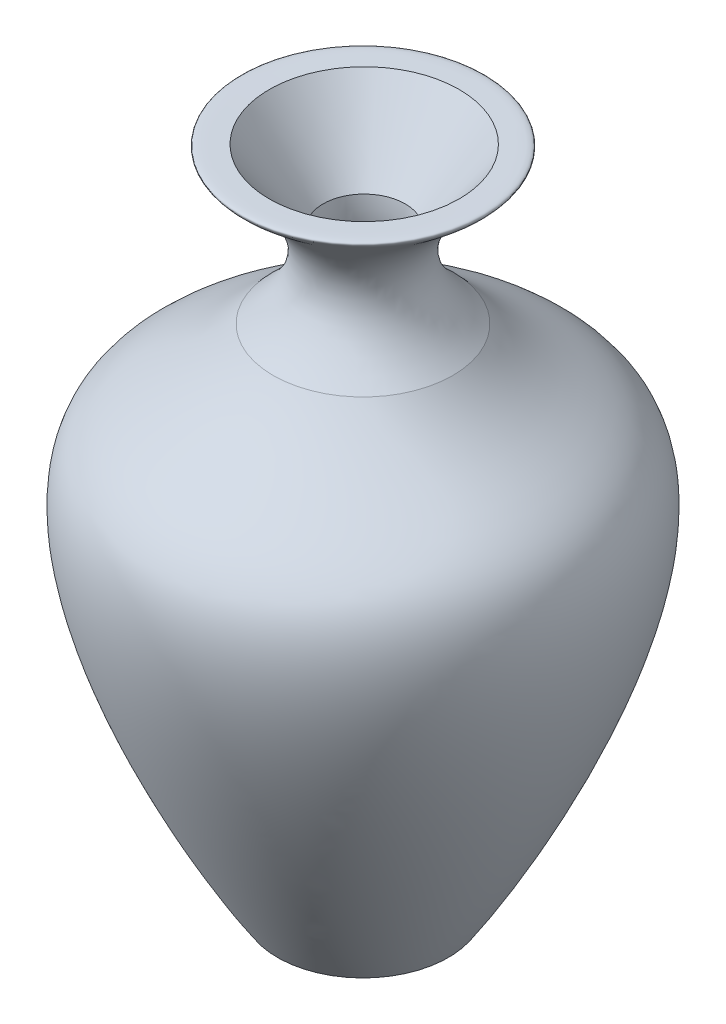
SolidWorks part; units mm, degrees
material "Ti-8Al-1Mo-1V annealed sheet (SS)"
ref_plane "Front Plane" through (0, 0, 0) normal (0, 0, 1) x (1, 0, 0)
ref_plane "Top Plane" through (0, 0, 0) normal (0, 1, 0) x (1, 0, 0)
ref_plane "Right Plane" through (0, 0, 0) normal (1, 0, 0) x (0, 0, -1)
sketch "Sketch1" plane through (0, 0, 0) normal (0, 0, 1) x (1, 0, 0)
  line L2 (-1.7649, 3.7152) -> (-5.8192, 3.7152)
  line L3 (-5.8192, 3.7152) -> (-5.8192, 35.1345)
  line L4 (-5.8192, 35.1345) -> (-2.4351, 35.1345)
  line L5 (-5.8192, 35.1345) -> (-5.8192, 1.8892) construction
  spline S0 degree 3 poles (-2.4351, 35.1345) (-0.3032, 35.0338) (1.6095, 35.8702) (-5.3828, 31.0399) (-1.562, 27.7204) knots 0 0 0 0 0.514505 1 1 1 1
  spline S1 degree 3 poles (-1.562, 27.7204) (0.5045, 25.3026) (9.1516, 23.4539) (0.9144, 7.7157) (-1.7649, 3.7152) knots 0 0 0 0 0.292039 1 1 1 1
revolve "Revolve1" add sketch "Sketch1" angle 360 about L5
sketch "Sketch2" plane through (0, 0, 0) normal (0, 0, 1) x (1, 0, 0)
  line L0 (-5.7622, 4.7898) -> (-5.7622, 37.5841) construction
  line L2 (-5.7622, 35.2831) -> (-1.1411, 35.2831)
  line L3 (-1.1411, 35.2831) -> (-3.8138, 31.6966)
  line L4 (-10.0764, 27.7204) -> (-1.562, 27.7204) construction
  line L5 (-2.9312, 4.7898) -> (-5.7622, 4.7898)
  line L6 (-5.7622, 4.7898) -> (-5.7622, 35.2831)
  spline S0 degree 2 poles (-3.8138, 31.6966) (-4.1922, 28.9696) (-2.3225, 27.7204) knots 0 0 0 1 1 1
  spline S1 degree 3 poles (-2.3225, 27.7204) (-0.7359, 26.4593) (6.4408, 19.7399) (-0.7536, 8.7782) (-2.9312, 4.7898) knots 0 0 0 0 0.258285 1 1 1 1
revolve "Cut-Revolve4" cut sketch "Sketch2" angle 360 about L0
